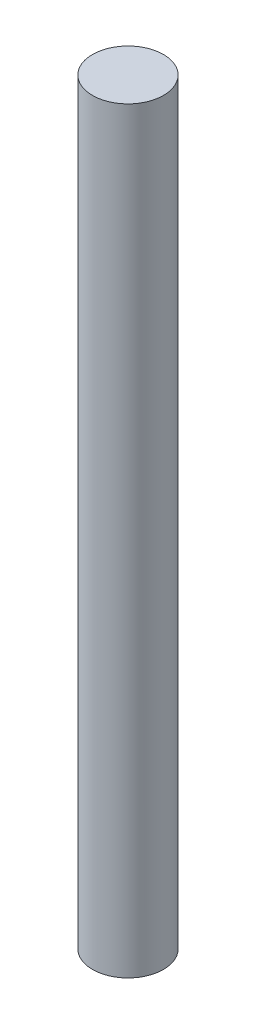
SolidWorks part; units mm, degrees
ref_plane "Front Plane" through (0, 0, 0) normal (0, 0, 1) x (1, 0, 0)
ref_plane "Top Plane" through (0, 0, 0) normal (0, 1, 0) x (1, 0, 0)
ref_plane "Right Plane" through (0, 0, 0) normal (1, 0, 0) x (0, 0, -1)
ref_plane "Plane1"
sketch "Sketch1" plane through (0, -7.6831, 0) normal (0, 0, 1) x (-1, 0, 0)
  line L0 (0, -7.6831) -> (1.5, -7.6831)
  line L1 (1.5, -7.6831) -> (1.5, 24.3169)
  line L2 (1.5, 24.3169) -> (0, 24.3169)
  line L3 (0, 24.3169) -> (0, -7.6831)
  line L4 (0, -7.6831) -> (0, 31.0323) construction
  dimension "D1" = 32
  dimension "D2" = 90
revolve "Revolution1" add sketch "Sketch1" angle 360 about L4
sketch "Sketch2" plane through (0, -32, 0) normal (0, -1, 0) x (1, 0, 0)
  line L0 (-1, -1.118) -> (-1, 1.118)
  arc A0 (-1, 1.118) -> (-1, -1.118) centre (0, 0) ccw
extrude "Extrusion1" cut sketch "Sketch2" against normal blind 9.3
